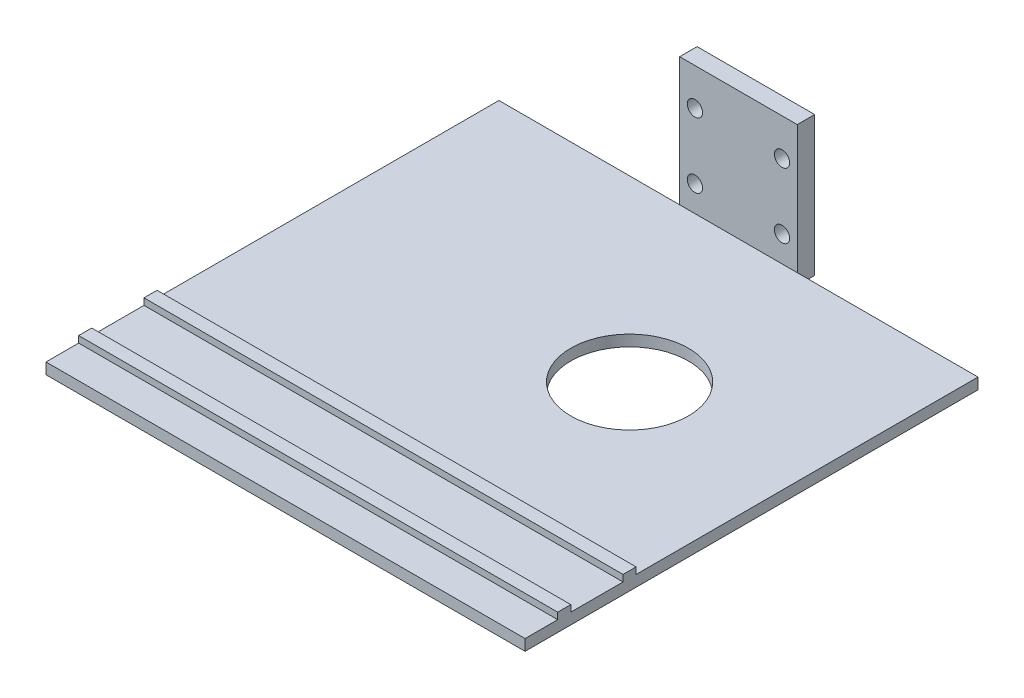
SolidWorks part; units mm, degrees
ref_plane "Piano frontale" through (0, 0, 0) normal (0, 0, 1) x (1, 0, 0)
ref_plane "Piano superiore" through (0, 0, 0) normal (0, 1, 0) x (1, 0, 0)
ref_plane "Piano destro" through (0, 0, 0) normal (1, 0, 0) x (0, 0, -1)
sketch "Schizzo1" plane through (0, 0, 0) normal (0, 0, 1) x (1, 0, 0)
  line L1 (0, 0) -> (27, 0)
  line L2 (0, 0) -> (0, -36)
  line L3 (0, -36) -> (27, -36)
  line L4 (27, 0) -> (27, -36)
  dimension "D1" = 27
  dimension "D2" = 36
extrude "Estrusione-Estrusione1" add sketch "Schizzo1" along normal blind 4
sketch "Schizzo10" plane through (0, 0, 4) normal (0, 0, 1) x (1, 0, 0)
  line L0 (27, 0) -> (0, 0) construction
  line L1 (3.5, -12.5) -> (23.5, -12.5) construction
  line L2 (3.5, -12.5) -> (3.5, -27.5) construction
  line L3 (3.5, -27.5) -> (23.5, -27.5) construction
  line L4 (23.5, -12.5) -> (23.5, -27.5) construction
  line L5 (27, -36) -> (27, 0) construction
  circle A0 centre (3.5, -12.5) radius 1.75
  circle A1 centre (23.5, -12.5) radius 1.75
  circle A2 centre (23.5, -27.5) radius 1.75
  circle A3 centre (3.5, -27.5) radius 1.75
  dimension "D5" = 3.5
  dimension "D1" = 12.5
  dimension "D2" = 15
  dimension "D3" = 20
  dimension "D4" = 3.5
extrude "Taglio-Estrusione5" cut sketch "Schizzo10" against normal blind 10
ref_plane "Piano1" through (13.5, 0, 0) normal (1, 0, 0) x (0, 0, -1)
sketch "Schizzo12" plane through (13.5, 0, 0) normal (1, 0, 0) x (0, 0, -1)
  line L1 (-4, -36) -> (-108, -36)
  line L2 (-4, -36) -> (-4, -33.4507)
  line L3 (-4, -33.4507) -> (-108, -33.4507)
  line L4 (-108, -36) -> (-108, -33.4507)
  dimension "D1" = 104
extrude "Estrusione-Estrusione2" add sketch "Schizzo12" along normal blind 55 and the other way blind 55
sketch "Schizzo14" plane through (-41.5, 0, 0) normal (-1, 0, 0) x (0, 0, 1)
  line L0 (4, -33.4507) -> (108, -33.4507) construction
  line L1 (82.5, -33.4507) -> (85.5, -33.4507)
  line L2 (82.5, -33.4507) -> (82.5, -31.9507)
  line L3 (82.5, -31.9507) -> (85.5, -31.9507)
  line L4 (85.5, -33.4507) -> (85.5, -31.9507)
  line L5 (108, -33.4507) -> (108, -36) construction
  line L6 (97.5, -33.4507) -> (100.5, -33.4507)
  line L7 (97.5, -33.4507) -> (97.5, -31.9507)
  line L8 (97.5, -31.9507) -> (100.5, -31.9507)
  line L9 (100.5, -33.4507) -> (100.5, -31.9507)
  dimension "D1" = 7.5
  dimension "D2" = 12
  dimension "D3" = 1.5
  dimension "D4" = 3
extrude "Estrusione-Estrusione3" add sketch "Schizzo14" against normal blind 110
sketch "Schizzo15" plane through (0, 0, 4) normal (0, 0, 1) x (1, 0, 0)
  line L0 (27, -33.4507) -> (27, 0) construction
  line L1 (0, 0) -> (27, 0)
  line L2 (0, 0) -> (0, -4)
  line L3 (0, -4) -> (27, -4)
  line L4 (27, 0) -> (27, -4)
  dimension "D1" = 4
extrude "Taglio-Estrusione6" cut sketch "Schizzo15" against normal through all
sketch "Schizzo16" plane through (0, -33.4507, 0) normal (0, 1, 0) x (1, 0, 0)
  line L0 (68.5, -45) -> (29.5, -45) construction
  line L1 (68.5, -4) -> (68.5, -82.5) construction
  line L2 (29.5, -4) -> (29.5, -45) construction
  line L3 (27, -4) -> (68.5, -4) construction
  circle A0 centre (29.5, -45) radius 13.5
  dimension "D3" = 27
  dimension "D1" = 39
  dimension "D2" = 41
extrude "Taglio-Estrusione7" cut sketch "Schizzo16" against normal blind 10
